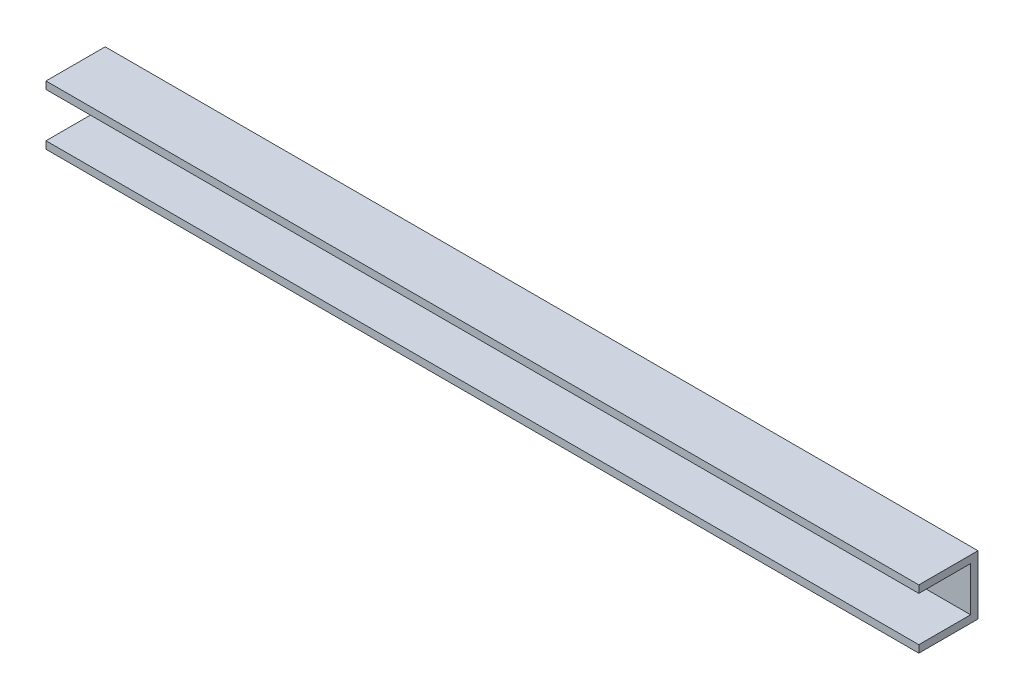
SolidWorks part; units mm, degrees
ref_plane "Front Plane" through (0, 0, 0) normal (0, 0, 1) x (1, 0, 0)
ref_plane "Top Plane" through (0, 0, 0) normal (0, 1, 0) x (1, 0, 0)
ref_plane "Right Plane" through (0, 0, 0) normal (1, 0, 0) x (0, 0, -1)
sketch "Sketch1" plane through (0, 0, 0) normal (1, 0, 0) x (0, 0, -1)
  line L1 (0, 0) -> (25.4, 0)
  line L2 (0, 0) -> (0, 25.4)
  line L3 (0, 25.4) -> (25.4, 25.4)
  line L4 (25.4, 0) -> (25.4, 25.4)
  dimension "D1" = 25.4
  dimension "D2" = 25.4
extrude "Boss-Extrude1" add sketch "Sketch1" along normal blind 374.65
sketch "Sketch2" plane through (0, 0, 0) normal (0, 0, 1) x (1, 0, 0)
  circle A0 centre (187.325, 12.7) radius 6.35
  dimension "D1" = 12.7
extrude "Cut-Extrude1" cut sketch "Sketch2" against normal through all
sketch "Sketch3" plane through (374.65, 0, 0) normal (1, 0, 0) x (0, 0, -1)
  line L0 (0, 25.4) -> (0, 0) construction
  line L1 (0, 22.225) -> (22.225, 22.225)
  line L2 (0, 22.225) -> (0, 3.175)
  line L3 (0, 3.175) -> (22.225, 3.175)
  line L4 (22.225, 22.225) -> (22.225, 3.175)
  line L5 (25.4, 25.4) -> (0, 25.4) construction
  line L6 (25.4, 0) -> (25.4, 25.4) construction
  line L7 (0, 0) -> (25.4, 0) construction
  dimension "D1" = 3.175
  dimension "D2" = 3.175
  dimension "D3" = 3.175
extrude "Cut-Extrude2" cut sketch "Sketch3" against normal through all
